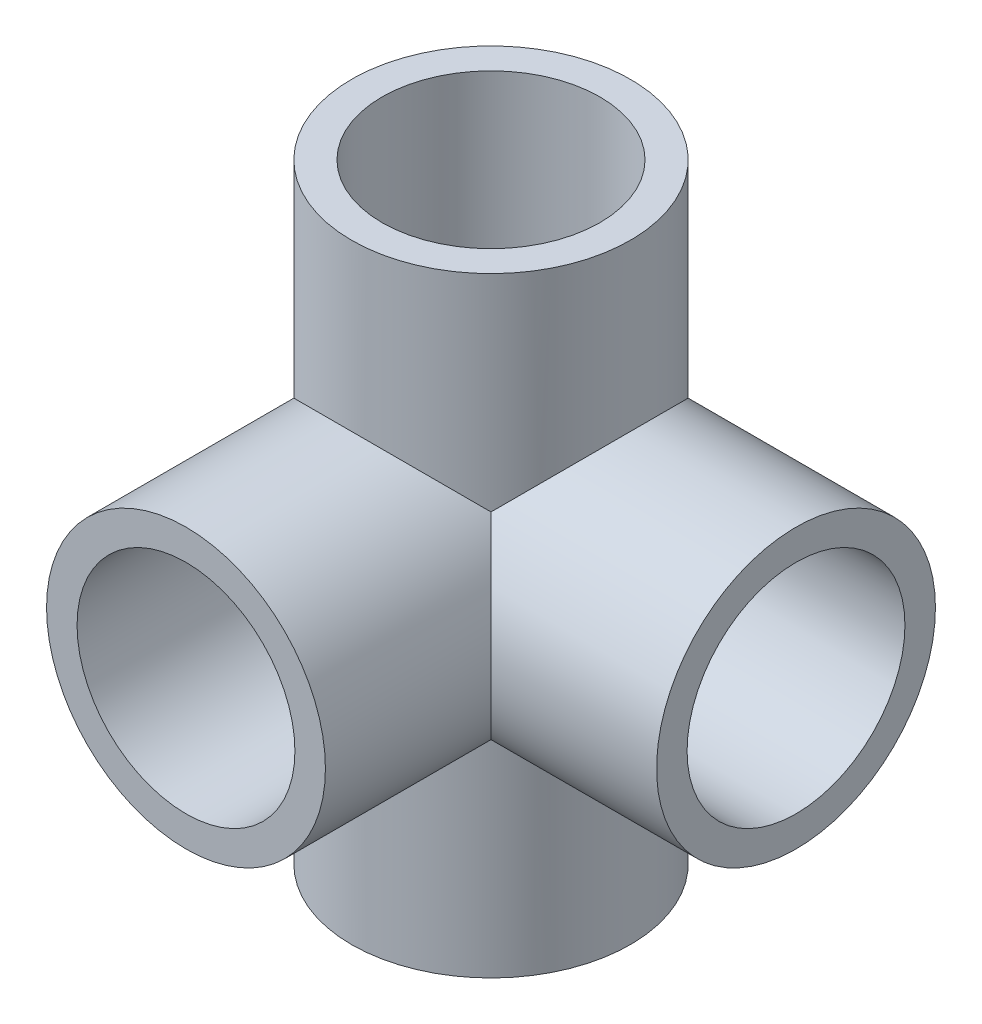
SolidWorks part; units mm, degrees
ref_plane "前视基准面" through (0, 0, 0) normal (0, 0, 1) x (1, 0, 0)
ref_plane "上视基准面" through (0, 0, 0) normal (0, 1, 0) x (1, 0, 0)
ref_plane "右视基准面" through (0, 0, 0) normal (1, 0, 0) x (0, 0, -1)
other "Configuration Table"
sketch "草图1" plane through (0, 0, 0) normal (0, 0, 1) x (1, 0, 0)
  circle A0 centre (0, 0) radius 12.5
  circle A1 centre (0, 0) radius 16
  dimension "D1" = 25
  dimension "D2" = 32
extrude "凸台-拉伸1" add sketch "草图1" along normal blind 35
sketch "草图2" plane through (0, 0, 0) normal (1, 0, 0) x (0, 0, -1)
  circle A0 centre (0, 0) radius 16
  circle A1 centre (0, 0) radius 12.5
  dimension "D1" = 32
  dimension "D2" = 25
extrude "凸台-拉伸2" add sketch "草图2" along normal blind 35
sketch "草图3" plane through (0, 0, 0) normal (0, 0, 1) x (1, 0, 0)
  line L0 (0, 16) -> (0, -16)
  arc A0 (0, 16) -> (0, -16) centre (0, 0) ccw
  circle A1 centre (0, 0) radius 16 construction
sketch "草图4" plane through (0, 0, 0) normal (0, 1, 0) x (1, 0, 0)
  circle A0 centre (0, 0) radius 16
  circle A1 centre (0, 0) radius 12.5
  dimension "D1" = 32
  dimension "D2" = 25
extrude "凸台-拉伸3" add sketch "草图4" along normal blind 35
revolve "旋转1" add sketch "草图3" angle 90 about L0
sketch "草图5" plane through (0, 0, 0) normal (0, 1, 0) x (1, 0, 0)
  circle A2 centre (0, 0) radius 12.5 construction
  circle A4 centre (0, 0) radius 12.5
  circle A5 centre (0, 0) radius 16 construction
  circle A7 centre (0, 0) radius 16
extrude "凸台-拉伸4" add sketch "草图5" against normal blind 35
